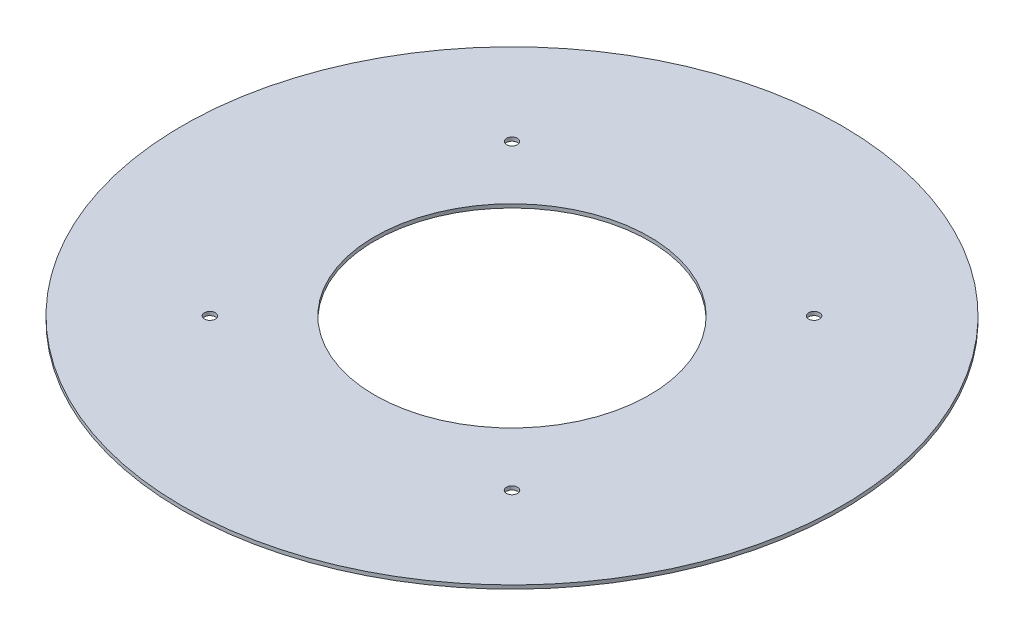
SolidWorks part; units mm, degrees
material "5052-H34"
ref_plane "Front Plane" through (0, 0, 0) normal (0, 0, 1) x (1, 0, 0)
ref_plane "Top Plane" through (0, 0, 0) normal (0, 1, 0) x (1, 0, 0)
ref_plane "Right Plane" through (0, 0, 0) normal (1, 0, 0) x (0, 0, -1)
sketch "Sketch1" plane through (0, 0, 0) normal (0, 1, 0) x (1, 0, 0)
  line L1 (-82.5, 82.5) -> (82.5, 82.5) construction
  line L2 (-82.5, 82.5) -> (-82.5, -82.5) construction
  line L3 (-82.5, -82.5) -> (82.5, -82.5) construction
  line L4 (82.5, 82.5) -> (82.5, -82.5) construction
  line L5 (-82.5, 82.5) -> (82.5, -82.5) construction
  line L6 (-82.5, -82.5) -> (82.5, 82.5) construction
  circle A1 centre (0, 0) radius 180
  circle A2 centre (0, 0) radius 75
  circle A3 centre (-82.5, 82.5) radius 3
  circle A4 centre (82.5, 82.5) radius 3
  circle A5 centre (82.5, -82.5) radius 3
  circle A6 centre (-82.5, -82.5) radius 3
  dimension "D1" = 150
  dimension "D3" = 165
  dimension "356" = 360
  dimension "D5" = 6
  dimension "D4" = 165
extrude "Boss-Extrude1" add sketch "Sketch1" along normal blind 2
